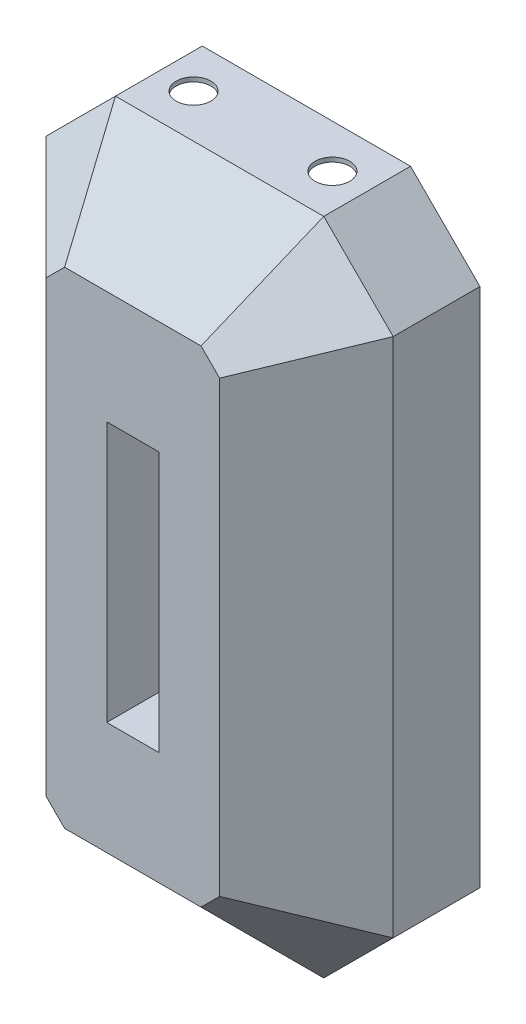
SolidWorks part; units mm, degrees
material "Balsa"
ref_plane "Front Plane" through (0, 0, 0) normal (0, 0, 1) x (1, 0, 0)
ref_plane "Top Plane" through (0, 0, 0) normal (0, 1, 0) x (1, 0, 0)
ref_plane "Right Plane" through (0, 0, 0) normal (1, 0, 0) x (0, 0, -1)
sketch "Sketch1" plane through (0, 0, 0) normal (0, 0, 1) x (1, 0, 0)
  line L0 (-152.4, 482.6) -> (-254, 381)
  line L1 (-152.4, 482.6) -> (152.4, 482.6)
  line L2 (-254, 381) -> (-254, -381)
  line L3 (-152.4, -482.6) -> (152.4, -482.6)
  line L4 (254, 381) -> (254, -381)
  line L5 (-254, 482.6) -> (254, -482.6) construction
  line L6 (-254, -482.6) -> (254, 482.6) construction
  line L7 (152.4, 482.6) -> (254, 381)
  line L8 (254, -381) -> (152.4, -482.6)
  line L9 (-254, -381) -> (-152.4, -482.6)
  line L10 (-149.7697, 476.25) -> (-247.65, 378.3697)
  line L11 (-247.65, 378.3697) -> (-247.65, -378.3697)
  line L12 (-247.65, -378.3697) -> (-149.7697, -476.25)
  line L13 (-149.7697, -476.25) -> (149.7697, -476.25)
  line L14 (247.65, -378.3697) -> (149.7697, -476.25)
  line L15 (247.65, 378.3697) -> (247.65, -378.3697)
  line L16 (149.7697, 476.25) -> (247.65, 378.3697)
  line L17 (-149.7697, 476.25) -> (149.7697, 476.25)
  point P1 (0, 0)
  point P6 (0, 0)
  dimension "D1" = 965.2
  dimension "D2" = 508
  dimension "D3" = 6.35
extrude "Boss-Extrude1" add sketch "Sketch1" along normal blind 127 contours L0 L2 L9 L3 L8 L4 L7 L1 | L10 L11 L12 L13 L14 L15 L16 L17
sketch "Sketch3" plane through (0, 0, 127) normal (0, 0, 1) x (1, 0, 0)
  line L0 (-152.4, 482.6) -> (152.4, 482.6)
  line L1 (152.4, 482.6) -> (254, 381)
  line L2 (254, 381) -> (254, -381)
  line L3 (254, -381) -> (152.4, -482.6)
  line L4 (152.4, -482.6) -> (-152.4, -482.6)
  line L5 (-152.4, -482.6) -> (-254, -381)
  line L6 (-254, -381) -> (-254, 381)
  line L7 (-254, 381) -> (-152.4, 482.6)
  line L8 (-149.7697, 476.25) -> (149.7697, 476.25)
  line L9 (149.7697, 476.25) -> (247.65, 378.3697)
  line L10 (247.65, 378.3697) -> (247.65, -378.3697)
  line L11 (247.65, -378.3697) -> (149.7697, -476.25)
  line L12 (149.7697, -476.25) -> (-149.7697, -476.25)
  line L13 (-149.7697, -476.25) -> (-247.65, -378.3697)
  line L14 (-247.65, -378.3697) -> (-247.65, 378.3697)
  line L15 (-247.65, 378.3697) -> (-149.7697, 476.25)
ref_plane "Plane2" through (0, 0, 254) normal (0, 0, 1) x (1, 0, 0)
sketch "Sketch4" plane through (0, 0, 254) normal (0, 0, 1) x (1, 0, 0)
  line L0 (-254, 381) -> (-152.4, 482.6)
  line L1 (-152.4, 482.6) -> (152.4, 482.6)
  line L2 (152.4, 482.6) -> (254, 381)
  line L3 (254, 381) -> (254, -381)
  line L4 (254, -381) -> (152.4, -482.6)
  line L5 (152.4, -482.6) -> (-152.4, -482.6)
  line L6 (-152.4, -482.6) -> (-254, -381)
  line L7 (-254, -381) -> (-254, 381)
  line L8 (-127, 328.3949) -> (-99.7949, 355.6)
  line L9 (-99.7949, 355.6) -> (99.7949, 355.6)
  line L10 (99.7949, 355.6) -> (127, 328.3949)
  line L11 (127, 328.3949) -> (127, -328.3949)
  line L12 (127, -328.3949) -> (99.7949, -355.6)
  line L13 (99.7949, -355.6) -> (-99.7949, -355.6)
  line L14 (-99.7949, -355.6) -> (-127, -328.3949)
  line L15 (-127, -328.3949) -> (-127, 328.3949)
  line L16 (-120.65, -325.7646) -> (-120.65, 325.7646)
  line L17 (-120.65, 325.7646) -> (-97.1646, 349.25)
  line L18 (-97.1646, 349.25) -> (97.1646, 349.25)
  line L19 (97.1646, 349.25) -> (120.65, 325.7646)
  line L20 (120.65, 325.7646) -> (120.65, -325.7646)
  line L21 (120.65, -325.7646) -> (97.1646, -349.25)
  line L22 (97.1646, -349.25) -> (-97.1646, -349.25)
  line L23 (-97.1646, -349.25) -> (-120.65, -325.7646)
  dimension "D1" = 127
  dimension "D2" = 6.35
loft "Loft3" add section "Sketch3" section "Sketch4"
sketch "Sketch5" plane through (0, 0, 254) normal (0, 0, 1) x (1, 0, 0)
  line L1 (-38.1, 190.5) -> (38.1, 190.5)
  line L2 (-38.1, 190.5) -> (-38.1, -190.5)
  line L3 (-38.1, -190.5) -> (38.1, -190.5)
  line L4 (38.1, 190.5) -> (38.1, -190.5)
  line L5 (-38.1, 190.5) -> (38.1, -190.5) construction
  line L6 (-38.1, -190.5) -> (38.1, 190.5) construction
  point P0 (0, 0)
  dimension "D1" = 381
  dimension "D2" = 76.2
extrude "Cut-Extrude1" cut sketch "Sketch5" against normal through all
sketch "Sketch6" plane through (0, 482.6, 0) normal (0, 1, 0) x (1, 0, 0)
  line L0 (101.6, -63.5) -> (-101.6, -63.5) construction
  line L1 (-152.4, 0) -> (152.4, 0) construction
  line L2 (0, -63.5) -> (0, 0) construction
  circle A0 centre (101.6, -63.5) radius 25.4
  circle A1 centre (-101.6, -63.5) radius 25.4
  point P4 (0, 0)
  dimension "D1" = 50.8
  dimension "D2" = 50.8
  dimension "D3" = 63.5
  dimension "D4" = 203.2
extrude "Cut-Extrude2" cut sketch "Sketch6" against normal up to surface (6.35 mm away) up to face at (0, 476.25, 63.5)
